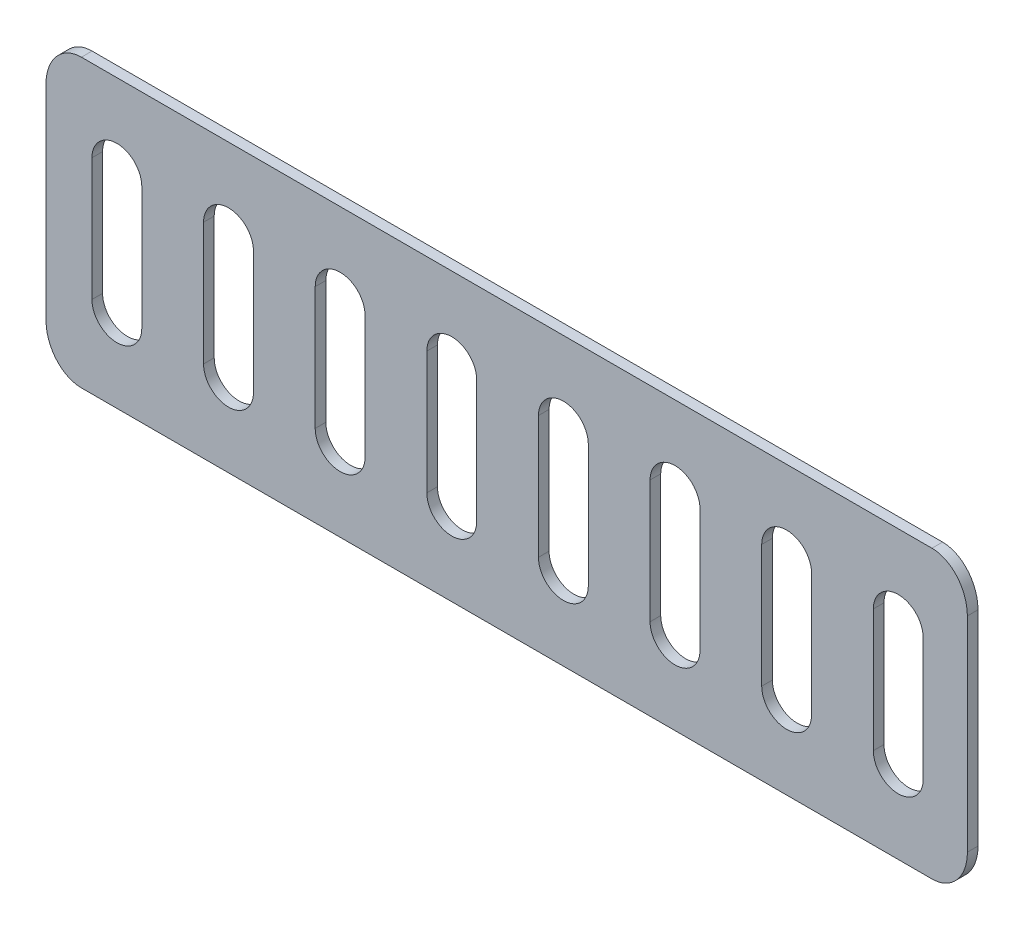
SolidWorks part; units mm, degrees
material "AISI 316 Stainless Steel Sheet (SS)"
ref_plane "Front Plane" through (0, 0, 0) normal (0, 0, 1) x (1, 0, 0)
ref_plane "Top Plane" through (0, 0, 0) normal (0, 1, 0) x (1, 0, 0)
ref_plane "Right Plane" through (0, 0, 0) normal (1, 0, 0) x (0, 0, -1)
sketch "Sketch1" plane through (0, 0, 0) normal (0, 0, 1) x (1, 0, 0)
  line L0 (120, 80.829) -> (-120, 80.829) construction
  line L1 (130, 150.1111) -> (130, 92.376) construction
  line L2 (-120, 161.6581) -> (120, 161.6581) construction
  line L3 (-130, 92.376) -> (-130, 150.1111) construction
  line L4 (120, 80.829) -> (-120, 80.829)
  line L5 (130, 150.1111) -> (130, 92.376)
  line L6 (-120, 161.6581) -> (120, 161.6581)
  line L7 (-130, 92.376) -> (-130, 150.1111)
  line L8 (-110, 138.5641) -> (-110, 103.923) construction
  line L9 (-102.9658, 138.5641) -> (-102.9658, 103.923)
  line L10 (-117.0342, 138.5641) -> (-117.0342, 103.923)
  line L11 (-85.5342, 138.5641) -> (-85.5342, 103.923)
  line L12 (-71.4658, 138.5641) -> (-71.4658, 103.923)
  line L13 (-78.5, 138.5641) -> (-78.5, 103.923) construction
  line L14 (-54.0342, 138.5641) -> (-54.0342, 103.923)
  line L15 (-39.9658, 138.5641) -> (-39.9658, 103.923)
  line L24 (-47, 138.5641) -> (-47, 103.923) construction
  line L25 (-22.5342, 138.5641) -> (-22.5342, 103.923)
  line L26 (-8.4658, 138.5641) -> (-8.4658, 103.923)
  line L27 (-15.5, 138.5641) -> (-15.5, 103.923) construction
  line L28 (8.9658, 138.5641) -> (8.9658, 103.923)
  line L29 (23.0342, 138.5641) -> (23.0342, 103.923)
  line L30 (16, 138.5641) -> (16, 103.923) construction
  line L31 (40.4658, 138.5641) -> (40.4658, 103.923)
  line L32 (54.5342, 138.5641) -> (54.5342, 103.923)
  line L33 (47.5, 138.5641) -> (47.5, 103.923) construction
  line L34 (71.9658, 138.5641) -> (71.9658, 103.923)
  line L35 (86.0342, 138.5641) -> (86.0342, 103.923)
  line L36 (79, 138.5641) -> (79, 103.923) construction
  line L37 (103.4658, 138.5641) -> (103.4658, 103.923)
  line L38 (117.5342, 138.5641) -> (117.5342, 103.923)
  line L39 (110.5, 138.5641) -> (110.5, 103.923) construction
  arc A0 (-102.9658, 138.5641) -> (-117.0342, 138.5641) centre (-110, 138.5641) ccw
  arc A1 (-117.0342, 103.923) -> (-102.9658, 103.923) centre (-110, 103.923) ccw
  arc A2 (-71.4658, 138.5641) -> (-85.5342, 138.5641) centre (-78.5, 138.5641) ccw
  arc A3 (-85.5342, 103.923) -> (-71.4658, 103.923) centre (-78.5, 103.923) ccw
  arc A4 (-39.9658, 138.5641) -> (-54.0342, 138.5641) centre (-47, 138.5641) ccw
  arc A5 (-54.0342, 103.923) -> (-39.9658, 103.923) centre (-47, 103.923) ccw
  arc A6 (-8.4658, 138.5641) -> (-22.5342, 138.5641) centre (-15.5, 138.5641) ccw
  arc A7 (-22.5342, 103.923) -> (-8.4658, 103.923) centre (-15.5, 103.923) ccw
  arc A8 (23.0342, 138.5641) -> (8.9658, 138.5641) centre (16, 138.5641) ccw
  arc A9 (8.9658, 103.923) -> (23.0342, 103.923) centre (16, 103.923) ccw
  arc A10 (54.5342, 138.5641) -> (40.4658, 138.5641) centre (47.5, 138.5641) ccw
  arc A11 (40.4658, 103.923) -> (54.5342, 103.923) centre (47.5, 103.923) ccw
  arc A12 (86.0342, 138.5641) -> (71.9658, 138.5641) centre (79, 138.5641) ccw
  arc A13 (71.9658, 103.923) -> (86.0342, 103.923) centre (79, 103.923) ccw
  arc A14 (117.5342, 138.5641) -> (103.4658, 138.5641) centre (110.5, 138.5641) ccw
  arc A15 (103.4658, 103.923) -> (117.5342, 103.923) centre (110.5, 103.923) ccw
  ellipse E0 centre (-120, 92.376) end of major axis (-120, 103.923) minor radius 10 (-130, 92.376) -> (-120, 80.829) ccw construction
  ellipse E1 centre (120, 92.376) end of major axis (120, 103.923) minor radius 10 (120, 80.829) -> (130, 92.376) ccw construction
  ellipse E2 centre (120, 150.1111) end of major axis (120, 161.6581) minor radius 10 (130, 150.1111) -> (120, 161.6581) ccw construction
  ellipse E3 centre (-120, 150.1111) end of major axis (-120, 161.6581) minor radius 10 (-120, 161.6581) -> (-130, 150.1111) ccw construction
  ellipse E4 centre (-120, 92.376) end of major axis (-120, 103.923) minor radius 10 (-130, 92.376) -> (-120, 80.829) ccw
  ellipse E5 centre (120, 92.376) end of major axis (120, 103.923) minor radius 10 (120, 80.829) -> (130, 92.376) ccw
  ellipse E6 centre (120, 150.1111) end of major axis (120, 161.6581) minor radius 10 (130, 150.1111) -> (120, 161.6581) ccw
  ellipse E7 centre (-120, 150.1111) end of major axis (-120, 161.6581) minor radius 10 (-120, 161.6581) -> (-130, 150.1111) ccw
  point P3 (-110, 121.2436)
  point P54 (-78.5, 121.2436)
  point P61 (-47, 121.2436)
  point P68 (-15.5, 121.2436)
  point P75 (16, 121.2436)
  point P82 (47.5, 121.2436)
  point P89 (79, 121.2436)
  point P96 (110.5, 121.2436)
  dimension "D1" = 7.0342
  dimension "D3" = 23.094
  dimension "D2" = 34.641
  dimension "D5" = 17.4315
  dimension "D4" = 8
extrude "Boss-Extrude1" add sketch "Sketch1" against normal blind 3
